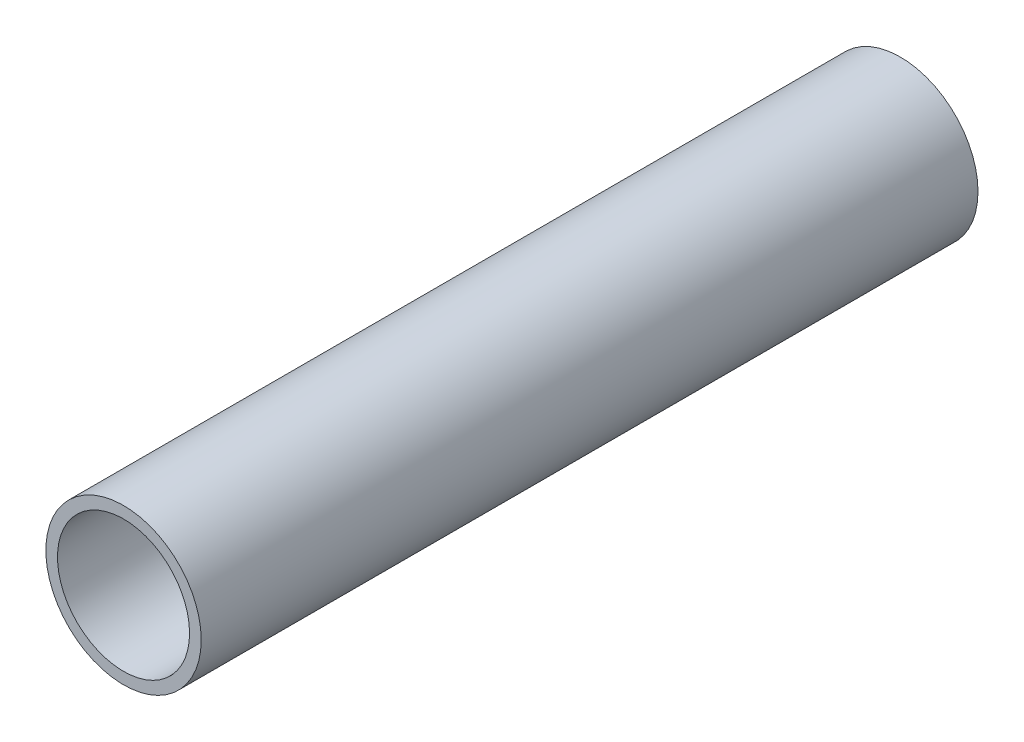
SolidWorks part; units mm, degrees
ref_plane "Front Plane" through (0, 0, 0) normal (0, 0, 1) x (1, 0, 0)
ref_plane "Top Plane" through (0, 0, 0) normal (0, 1, 0) x (1, 0, 0)
ref_plane "Right Plane" through (0, 0, 0) normal (1, 0, 0) x (0, 0, -1)
sketch "Sketch1" plane through (0, 0, 0) normal (0, 0, 1) x (1, 0, 0)
  circle A0 centre (0, 0) radius 30
  circle A2 centre (0, 0) radius 25.5
  dimension "D1" = 60
  dimension "D2" = 4.5
extrude "Boss-Extrude1" add sketch "Sketch1" along normal blind 300
